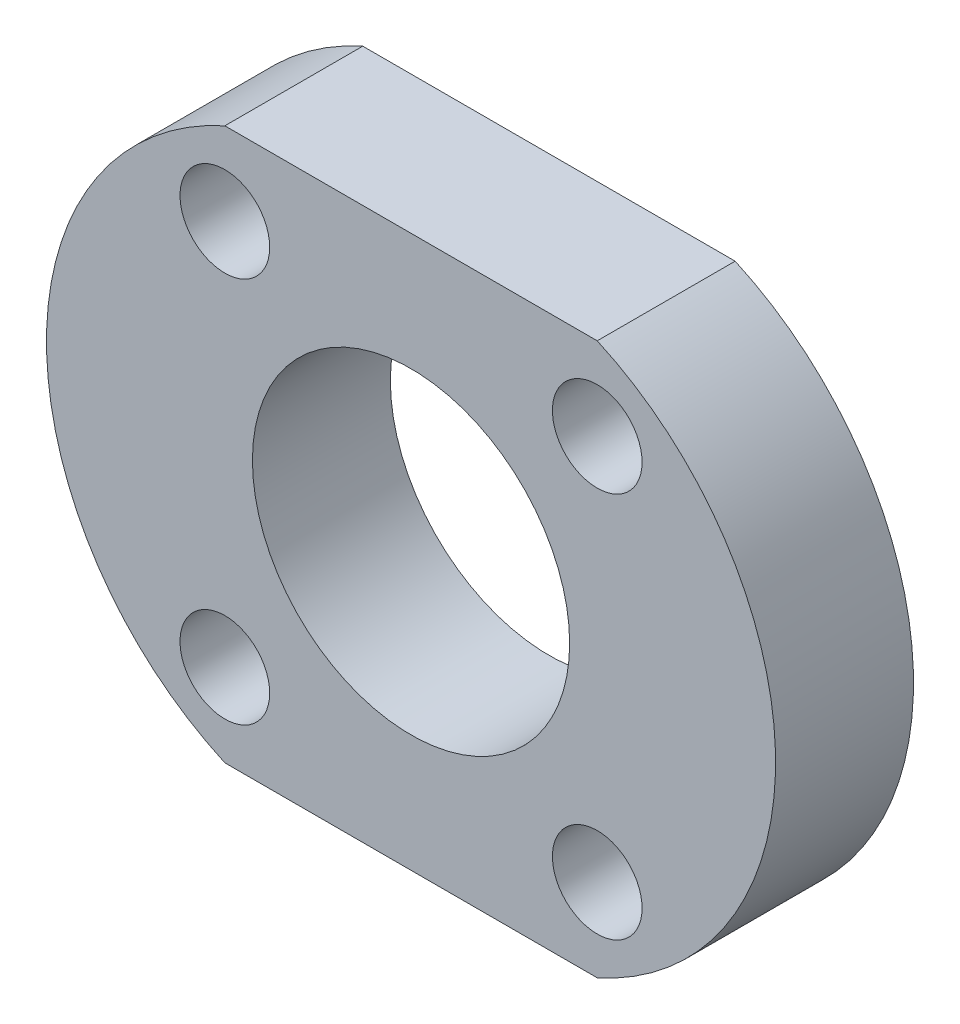
SolidWorks part; units mm, degrees
material "1.0037 (S235JR)"
ref_plane "Front Plane" through (0, 0, 0) normal (0, 0, 1) x (1, 0, 0)
ref_plane "Top Plane" through (0, 0, 0) normal (0, 1, 0) x (1, 0, 0)
ref_plane "Right Plane" through (0, 0, 0) normal (1, 0, 0) x (0, 0, -1)
sketch "Sketch2" plane through (0, 0, 0) normal (0, 0, 1) x (1, 0, 0)
  line L1 (-13.5, 20) -> (13.5, 20)
  line L3 (-13.5, -20) -> (13.5, -20)
  line L5 (-13.5, 20) -> (13.5, -20) construction
  line L6 (-13.5, -20) -> (13.5, 20) construction
  arc A0 (13.5, 20) -> (13.5, -20) centre (4.5, 0) cw
  arc A1 (-13.5, 20) -> (-13.5, -20) centre (-4.5, 0) ccw
  point P0 (0, 0)
  dimension "D1" = 27
  dimension "D2" = 40
  dimension "D3" = 9
  dimension "D4" = 9
extrude "Boss-Extrude1" add sketch "Sketch2" along normal blind 10
sketch "Sketch3" plane through (0, 0, 10) normal (0, 0, 1) x (1, 0, 0)
  circle A0 centre (0, 0) radius 11.5
  dimension "D1" = 23
extrude "Cut-Extrude1" cut sketch "Sketch3" against normal through all
sketch "Sketch4" plane through (0, 0, 10) normal (0, 0, 1) x (1, 0, 0)
  line L0 (-13.5, -20) -> (13.5, -20) construction
  line L1 (13.5, 20) -> (-13.5, 20) construction
  circle A0 centre (-13.5, 14) radius 3.25
  circle A1 centre (-13.5, -14) radius 3.25
  circle A2 centre (13.5, -14) radius 3.25
  circle A3 centre (13.5, 14) radius 3.25
  dimension "D1" = 6.5
  dimension "D2" = 6.5
  dimension "D3" = 6.5
  dimension "D4" = 6.5
  dimension "D5" = 6
  dimension "D6" = 6
  dimension "D7" = 6
  dimension "D8" = 6
extrude "Cut-Extrude2" cut sketch "Sketch4" against normal through all
